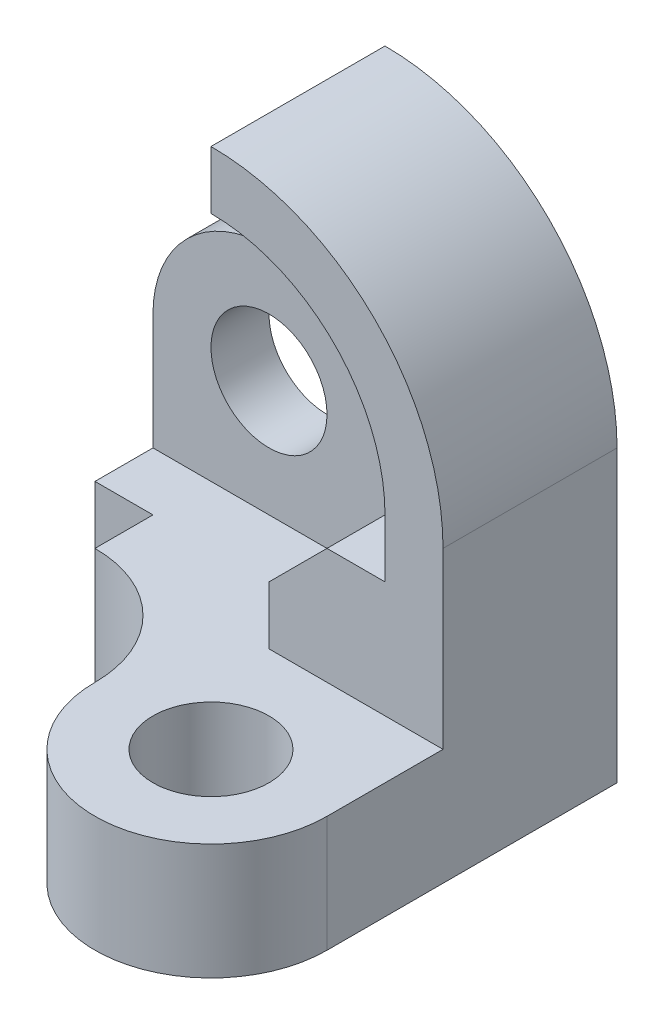
SolidWorks part; units mm, degrees
ref_plane "Front Plane" through (0, 0, 0) normal (0, 0, 1) x (1, 0, 0)
ref_plane "Top Plane" through (0, 0, 0) normal (0, 1, 0) x (1, 0, 0)
ref_plane "Right Plane" through (0, 0, 0) normal (1, 0, 0) x (0, 0, -1)
sketch "Sketch1" plane through (0, 0, 0) normal (0, 0, 1) x (1, 0, 0)
  line L0 (0, 30) -> (0, 40)
  line L1 (30, 0) -> (30, -10)
  line L2 (30, -10) -> (20, -10)
  line L3 (10, -20) -> (10, -30)
  line L4 (10, -30) -> (40, -30)
  line L5 (40, -30) -> (40, 0)
  line L6 (20, -10) -> (10, -20)
  arc A0 (40, 0) -> (0, 40) centre (0, 0) ccw
  arc A1 (30, 0) -> (0, 30) centre (0, 0) ccw
  point P0 (0, 0)
  dimension "D1" = 40
  dimension "D2" = 30
  dimension "D3" = 10
  dimension "D4" = 10
  dimension "D5" = 10
  dimension "D6" = 30
  dimension "D7" = 10
  dimension "D8" = 10
extrude "Boss-Extrude1" add sketch "Sketch1" along normal blind 30
sketch "Sketch2" plane through (0, 0, 0) normal (0, 0, 1) x (1, 0, 0)
  line L0 (0, 40) -> (0, 10)
  line L1 (0, 10) -> (-10, 10)
  line L2 (-30, -10) -> (-30, -50)
  line L3 (-30, -50) -> (40, -50)
  line L4 (40, -30) -> (40, 0) construction
  line L5 (40, 0) -> (40, -50)
  arc A0 (-10, 10) -> (-30, -10) centre (-10, -10) ccw
  arc A1 (0, 40) -> (40, 0) centre (0, 0) cw
  circle A2 centre (-10, -10) radius 10
  dimension "D2" = 20
  dimension "D5" = 20
  dimension "D1" = 30
  dimension "D3" = 40
  dimension "D4" = 70
extrude "Boss-Extrude2" add sketch "Sketch2" along normal blind 10
sketch "Sketch3" plane through (0, 0, 10) normal (0, 0, 1) x (1, 0, 0)
  line L1 (40, -30) -> (-30, -30)
  line L2 (40, -30) -> (40, -50)
  line L3 (40, -50) -> (-30, -50)
  line L4 (-30, -30) -> (-30, -50)
extrude "Boss-Extrude3" add sketch "Sketch3" along normal blind 70
sketch "Sketch4" plane through (0, -30, 0) normal (0, 1, 0) x (1, 0, 0)
  line L0 (40, -80) -> (40, -30) construction
  line L1 (-20, -30) -> (-20, -20)
  line L2 (-20, -20) -> (-30, -20)
  line L3 (-30, -20) -> (-30, -80)
  line L4 (-30, -80) -> (40, -80)
  line L5 (40, -80) -> (40, -50)
  arc A0 (40, -50) -> (0, -50) centre (20, -50) cw
  arc A1 (0, -50) -> (-20, -30) centre (-20, -50) ccw
  point P0 (40, -50)
  point P1 (20, -50)
  point P8 (-20, -50)
  dimension "D1" = 20
  dimension "D2" = 20
  dimension "D3" = 20
  dimension "D4" = 10
  dimension "D5" = 10
sketch "Sketch5" plane through (0, -30, 0) normal (0, 1, 0) x (1, 0, 0)
extrude "Cut-Extrude1" cut sketch "Sketch4" against normal blind 50
sketch "Sketch6" plane through (0, -30, 0) normal (0, 1, 0) x (1, 0, 0)
  line L1 (0, -30) -> (40, -30) construction
  circle A0 centre (20, -50) radius 10
  point P5 (20.9151, -30)
  dimension "D3" = 20
  dimension "D1" = 20
  dimension "D2" = 20
extrude "Cut-Extrude2" cut sketch "Sketch6" against normal blind 50
